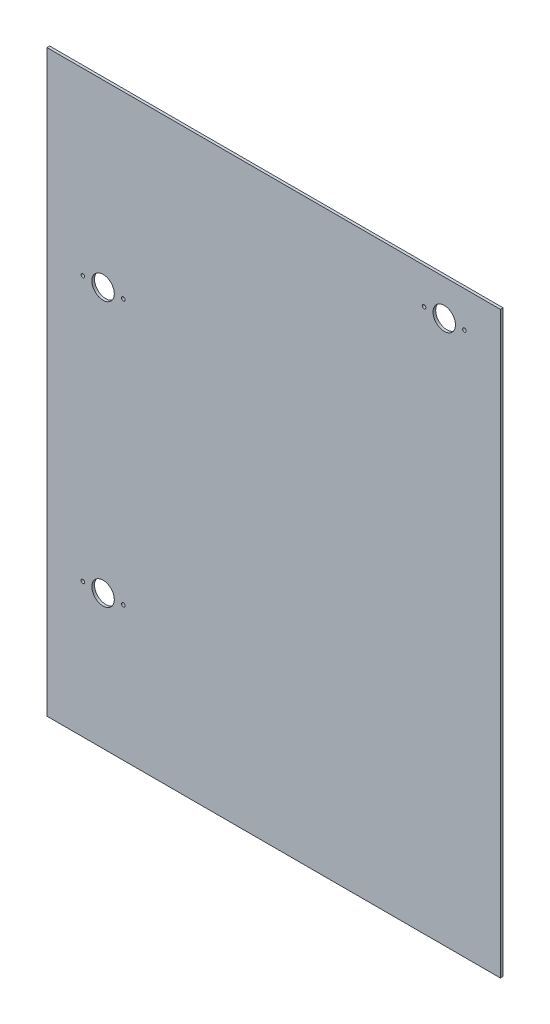
SolidWorks part; units mm, degrees
ref_plane "Přední rovina" through (0, 0, 0) normal (0, 0, 1) x (1, 0, 0)
ref_plane "Horní rovina" through (0, 0, 0) normal (0, 1, 0) x (1, 0, 0)
ref_plane "Pravá rovina" through (0, 0, 0) normal (1, 0, 0) x (0, 0, -1)
sketch "Skica1" plane through (0, 0, 0) normal (0, 0, 1) x (1, 0, 0)
  line L1 (-252.5, 322.5) -> (252.5, 322.5)
  line L2 (-252.5, 322.5) -> (-252.5, -322.5)
  line L3 (-252.5, -322.5) -> (252.5, -322.5)
  line L4 (252.5, 322.5) -> (252.5, -322.5)
  line L5 (-252.5, 322.5) -> (252.5, -322.5) construction
  line L6 (-252.5, -322.5) -> (252.5, 322.5) construction
  circle A0 centre (-212.5, -172.5) radius 2
  circle A1 centre (-190, -172.5) radius 12.5
  circle A2 centre (-167.5, -172.5) radius 2
  circle A3 centre (-212.5, 122.5) radius 2
  circle A4 centre (-190, 122.5) radius 12.5
  circle A5 centre (-167.5, 122.5) radius 2
  circle A6 centre (167.5, 282.5) radius 2
  circle A7 centre (190, 282.5) radius 12.5
  circle A8 centre (212.5, 282.5) radius 2
  point P0 (0, 0)
  point P24 (0, 0)
  dimension "D3" = 4
  dimension "D4" = 25
  dimension "D5" = 22.5
  dimension "D6" = 22.5
  dimension "D7" = 22.5
  dimension "D8" = 22.5
  dimension "D9" = 22.5
  dimension "D10" = 22.5
  dimension "D11" = 40
  dimension "D12" = 40
  dimension "D13" = 150
  dimension "D14" = 200
  dimension "D15" = 40
  dimension "D16" = 40
  dimension "D1" = 505
  dimension "D2" = 645
extrude "Přidat vysunutím1" add sketch "Skica1" along normal blind 3
